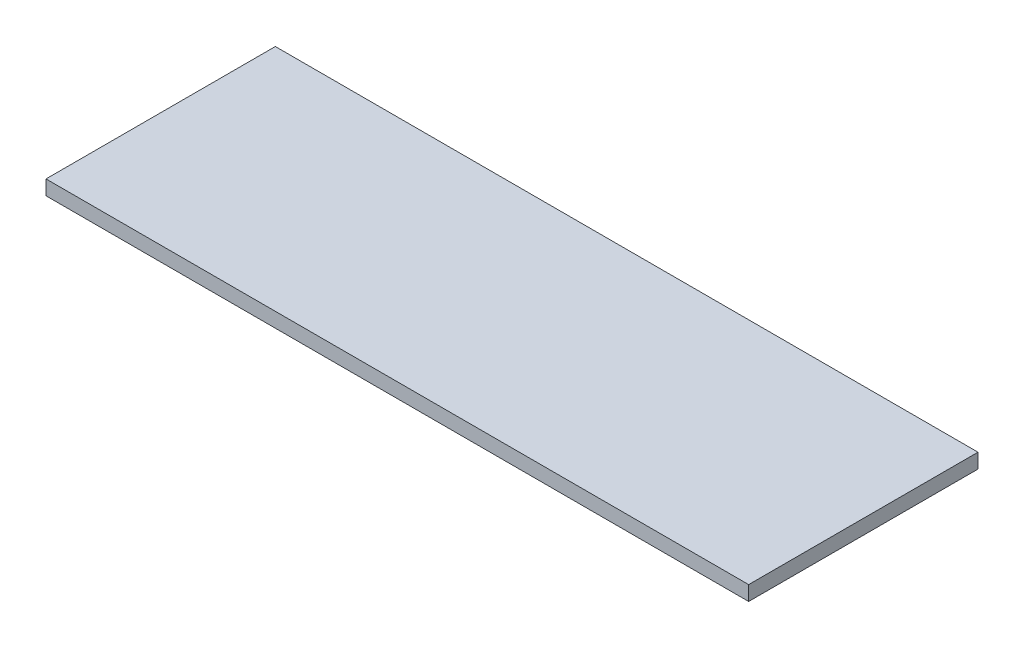
SolidWorks part; units mm, degrees
ref_plane "Front Plane" through (0, 0, 0) normal (0, 0, 1) x (1, 0, 0)
ref_plane "Top Plane" through (0, 0, 0) normal (0, 1, 0) x (1, 0, 0)
ref_plane "Right Plane" through (0, 0, 0) normal (1, 0, 0) x (0, 0, -1)
sketch "Sketch1" plane through (0, 0, 0) normal (0, 1, 0) x (1, 0, 0)
  line L1 (0, 0) -> (288, 0)
  line L2 (0, 0) -> (0, 94)
  line L3 (0, 94) -> (288, 94)
  line L4 (288, 0) -> (288, 94)
  dimension "D1" = 94
  dimension "D2" = 288
extrude "Boss-Extrude1" add sketch "Sketch1" along normal blind 6
